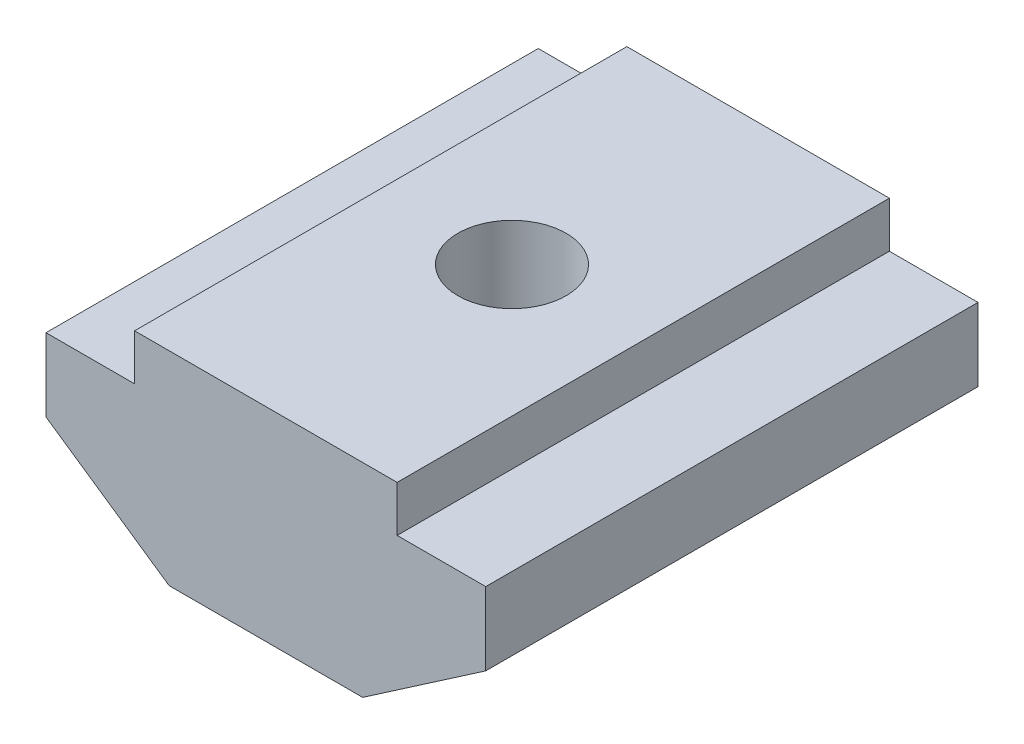
SolidWorks part; units mm, degrees
ref_plane "Спереди" through (0, 0, 0) normal (0, 0, 1) x (1, 0, 0)
ref_plane "Сверху" through (0, 0, 0) normal (0, 1, 0) x (1, 0, 0)
ref_plane "Справа" through (0, 0, 0) normal (1, 0, 0) x (0, 0, -1)
sketch "Эскиз1" plane through (0, 0, 0) normal (0, 0, 1) x (1, 0, 0)
  line L0 (4, 0) -> (-4, 0)
  line L1 (-4, 0) -> (-4, -1.4)
  line L2 (-4, -1.4) -> (-6.7, -1.4)
  line L3 (-6.7, -1.4) -> (-6.7, -3.6252)
  line L4 (-6.7, -3.6252) -> (-2.9486, -6.2)
  line L5 (-2.9486, -6.2) -> (2.9486, -6.2)
  line L6 (0, 0) -> (0, -6.2) construction
  line L7 (6.7, -3.6252) -> (2.9486, -6.2)
  line L8 (6.7, -1.4) -> (6.7, -3.6252)
  line L9 (4, -1.4) -> (6.7, -1.4)
  line L10 (4, 0) -> (4, -1.4)
  dimension "D1" = 4
  dimension "D2" = 1.4
  dimension "D3" = 6.7
  dimension "D4" = 4.8
extrude "Бобышка-Вытянуть1" add sketch "Эскиз1" along normal mid plane 15
hole_wizard "Отверстие обработанное метчиком M41" positions "Трехмерный эскиз1" profile "Эскиз2" tap size "M4" standard "DIN" end condition through all
sketch3d "Трехмерный эскиз1"
  point P0 (0, 0, 0)
  point P4 (0, 0, 0)
  point P7 (0, 0, 0)
sketch "Эскиз2" plane through (0, 0, 0) normal (1, 0, 0) x (0, 0, 1)
  line L0 (0, 0) -> (0, 6.2)
  line L1 (0, 6.2) -> (1.65, 6.2)
  line L2 (1.65, 6.2) -> (1.65, 0)
  line L5 (1.65, 0) -> (0, 0)
  line L11 (0, -6.35) -> (0, 107.95) construction
  dimension "Диаметр проходного сверла" = 3.3
  dimension "Глубина проходного сверла" = 6.2
cosmetic thread "Отверстие резьбы2" parameters "D2"=4
